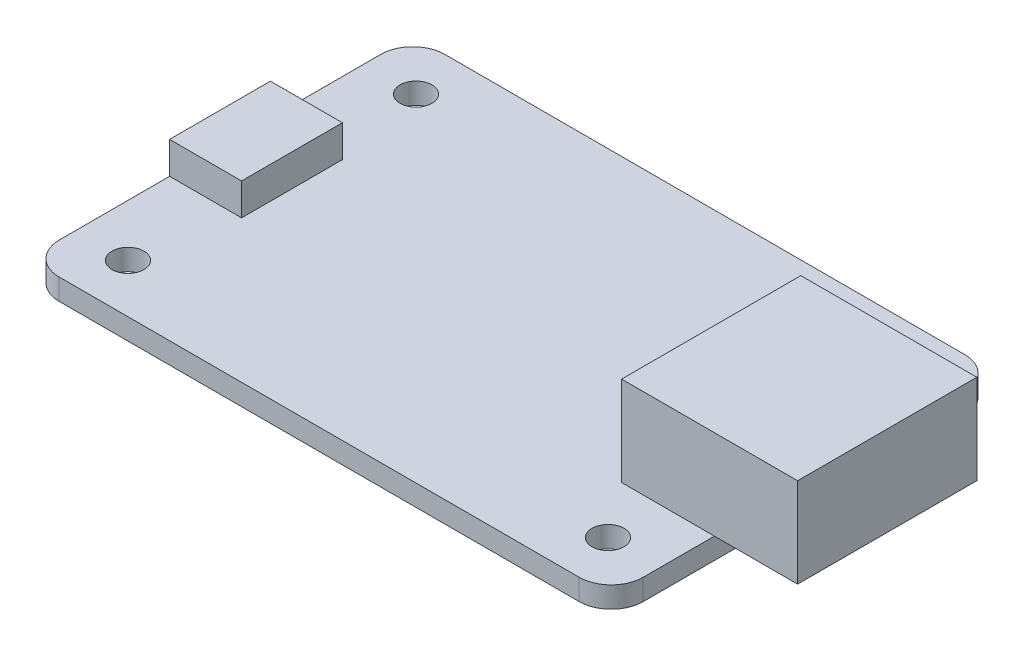
SolidWorks part; units mm, degrees
ref_plane "Front Plane" through (0, 0, 0) normal (0, 0, 1) x (1, 0, 0)
ref_plane "Top Plane" through (0, 0, 0) normal (0, 1, 0) x (1, 0, 0)
ref_plane "Right Plane" through (0, 0, 0) normal (1, 0, 0) x (0, 0, -1)
sketch "Sketch1" plane through (0, 0, 0) normal (0, 1, 0) x (1, 0, 0)
  line L0 (0, 30.607) -> (46.355, 0) construction
  line L1 (0, 0) -> (46.355, 0)
  line L2 (0, 0) -> (0, 30.607)
  line L3 (0, 30.607) -> (46.355, 30.607)
  line L4 (46.355, 0) -> (46.355, 30.607)
  line L5 (46.355, 30.607) -> (0, 0) construction
  line L7 (4.1275, 3.8735) -> (42.2275, 3.8735) construction
  line L8 (4.1275, 3.8735) -> (4.1275, 26.7335) construction
  line L9 (4.1275, 26.7335) -> (42.2275, 26.7335) construction
  line L10 (42.2275, 3.8735) -> (42.2275, 26.7335) construction
  line L11 (4.1275, 3.8735) -> (42.2275, 26.7335) construction
  line L12 (4.1275, 26.7335) -> (42.2275, 3.8735) construction
  circle A0 centre (4.1275, 26.7335) radius 1.27
  circle A1 centre (42.2275, 26.7335) radius 1.27
  circle A2 centre (4.1275, 3.8735) radius 1.27
  circle A3 centre (42.2275, 3.8735) radius 1.27
  point P5 (23.1775, 15.3035)
  dimension "D5" = 2.54
  dimension "D1" = 30.607
  dimension "D2" = 46.355
  dimension "D3" = 38.1
  dimension "D4" = 22.86
extrude "Boss-Extrude1" add sketch "Sketch1" along normal blind 1.6764
sketch "Sketch2" plane through (0, 1.6764, 0) normal (0, 1, 0) x (1, 0, 0)
  line L0 (46.355, 15.3035) -> (45.974, 15.3035) construction
  line L1 (46.355, 0) -> (46.355, 30.607) construction
  line L3 (38.989, 8.1915) -> (52.959, 8.1915)
  line L4 (38.989, 8.1915) -> (38.989, 22.4155)
  line L5 (38.989, 22.4155) -> (52.959, 22.4155)
  line L6 (52.959, 8.1915) -> (52.959, 22.4155)
  line L7 (38.989, 8.1915) -> (52.959, 22.4155) construction
  line L8 (38.989, 22.4155) -> (52.959, 8.1915) construction
  dimension "D1" = 14.224
  dimension "D2" = 13.97
  dimension "D3" = 6.604
extrude "Boss-Extrude2" add sketch "Sketch2" along normal blind 7.112
sketch "Sketch3" plane through (0, 1.6764, 0) normal (0, 1, 0) x (1, 0, 0)
  line L0 (0, 15.3035) -> (2.8575, 15.3035) construction
  line L1 (0, 30.607) -> (0, 0) construction
  line L3 (5.715, 19.304) -> (0, 19.304)
  line L4 (5.715, 19.304) -> (5.715, 11.303)
  line L5 (5.715, 11.303) -> (0, 11.303)
  line L6 (0, 19.304) -> (0, 11.303)
  line L7 (5.715, 19.304) -> (0, 11.303) construction
  line L8 (5.715, 11.303) -> (0, 19.304) construction
  dimension "D1" = 8.001
  dimension "D2" = 5.715
extrude "Boss-Extrude3" add sketch "Sketch3" along normal blind 2.54
fillet "Fillet1" radius 2.54 4 edges at (46.355, 0.8382, 0) (0, 0.8382, 0) (0, 0.8382, -30.607) (46.355, 0.8382, -30.607)
